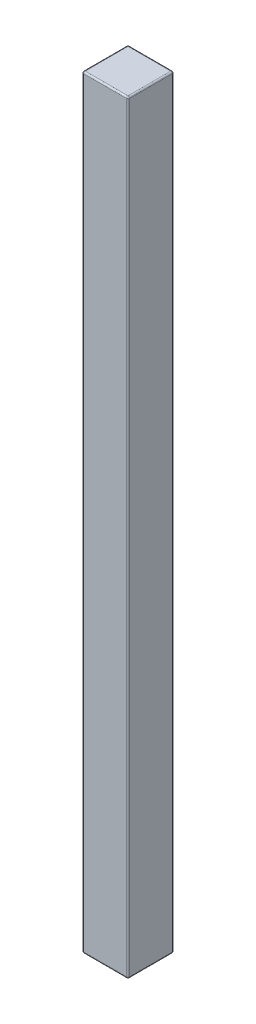
SolidWorks part; units mm, degrees
ref_plane "Plan de face" through (0, 0, 0) normal (0, 0, 1) x (1, 0, 0)
ref_plane "Plan de dessus" through (0, 0, 0) normal (0, 1, 0) x (1, 0, 0)
ref_plane "Plan de droite" through (0, 0, 0) normal (1, 0, 0) x (0, 0, -1)
sketch "Esquisse1" plane through (0, 0, 0) normal (0, 1, 0) x (1, 0, 0)
  line L1 (-1.5, -1.5) -> (1.5, -1.5)
  line L2 (-1.5, -1.5) -> (-1.5, 1.5)
  line L3 (-1.5, 1.5) -> (1.5, 1.5)
  line L4 (1.5, -1.5) -> (1.5, 1.5)
  line L5 (-1.5, -1.5) -> (1.5, 1.5) construction
  line L6 (-1.5, 1.5) -> (1.5, -1.5) construction
  point P0 (0, 0)
  dimension "D1" = 3
extrude "Boss.-Extru.1" add sketch "Esquisse1" along normal blind 50
fillet "Congé1" radius 0.1 12 edges at (1.5, 25, -1.5) (-1.5, 25, -1.5) (-1.5, 25, 1.5) (1.5, 25, 1.5) (0, 50, 1.5) (-1.5, 50, 0) (0, 50, -1.5) (1.5, 50, 0) (0, 0, 1.5) (-1.5, 0, 0) (0, 0, -1.5) (1.5, 0, 0)
